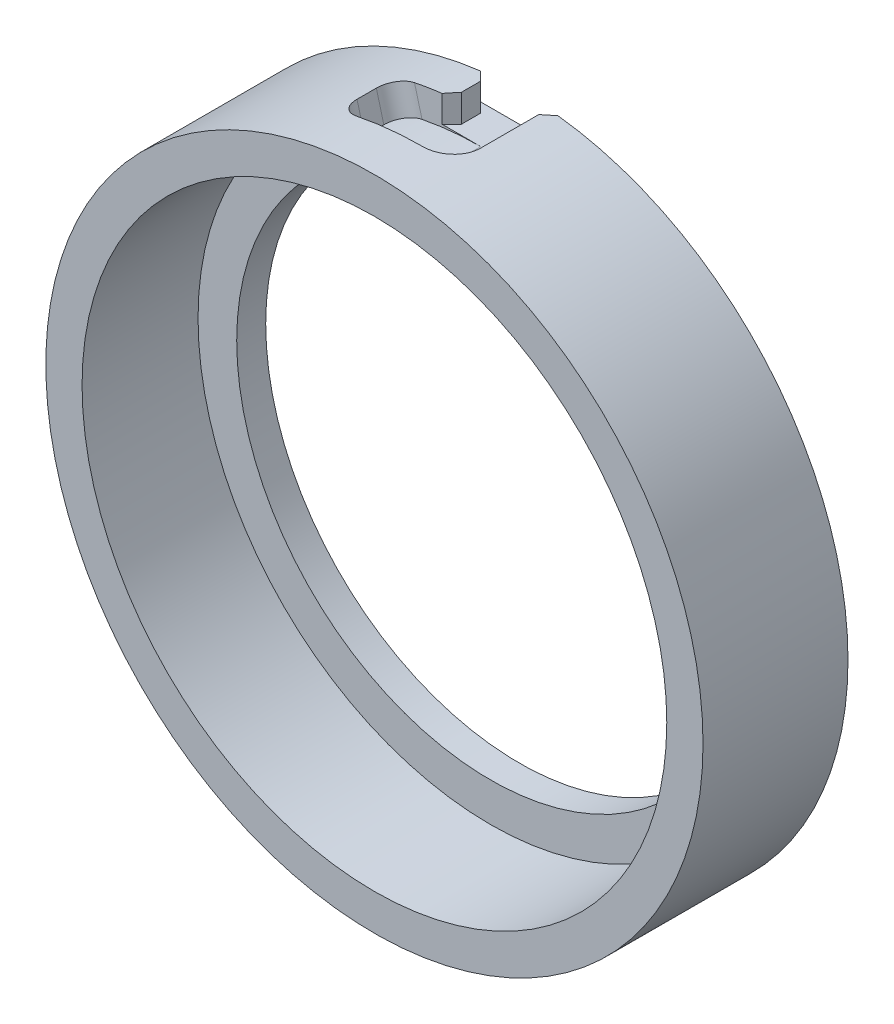
SolidWorks part; units mm, degrees
ref_plane "Спереди" through (0, 0, 0) normal (0, 0, 1) x (1, 0, 0)
ref_plane "Сверху" through (0, 0, 0) normal (0, 1, 0) x (1, 0, 0)
ref_plane "Справа" through (0, 0, 0) normal (1, 0, 0) x (0, 0, -1)
sketch "Эскиз2" plane through (0, 0, 0) normal (1, 0, 0) x (0, 0, -1)
  line L0 (0, 30.25) -> (0, 0) construction
  line L1 (0, 0) -> (15, 0) construction
  line L2 (0, 30.25) -> (12, 30.25)
  line L3 (12, 30.25) -> (12, 26.25)
  line L4 (12, 26.25) -> (15, 26.25)
  line L5 (15, 26.25) -> (15, 34)
  line L6 (15, 34) -> (0, 34)
  line L7 (0, 34) -> (0, 30.25)
  line L8 (15, 0) -> (15, 26.25) construction
  dimension "D1" = 60.5
  dimension "D2" = 68
  dimension "D3" = 15
  dimension "D4" = 4
  dimension "D5" = 3
revolve "Повернуть1" add sketch "Эскиз2" angle 360 about L1
ref_plane "Плоскость1" through (0, 34, 0) normal (0, 1, 0) x (1, 0, 0)
ref_plane "Плоскость2" through (0, -34, 0) normal (0, -1, 0) x (-1, 0, 0)
sketch "Эскиз4" plane through (0, 34, 0) normal (0, 1, 0) x (1, 0, 0)
  line L0 (0, 15) -> (0, 8) construction
  line L1 (34, 15) -> (-34, 15) construction
  line L2 (3, 15) -> (3, 8)
  line L3 (-3, 15) -> (-3, 8)
  arc A0 (3, 15) -> (-3, 15) centre (0, 15) ccw
  arc A1 (-3, 8) -> (3, 8) centre (0, 8) ccw
  point P5 (0, 11.5)
  dimension "D1" = 3
  dimension "D2" = 7
extrude "Вырез-Вытянуть1" cut sketch "Эскиз4" against normal blind 3
sketch "Эскиз5" plane through (0, -34, 0) normal (0, -1, 0) x (-1, 0, 0)
  line L0 (0, 15) -> (0, 8) construction
  line L1 (34, 15) -> (-34, 15) construction
  line L2 (3, 15) -> (3, 8)
  line L3 (-3, 15) -> (-3, 8)
  arc A0 (3, 15) -> (-3, 15) centre (0, 15) ccw
  arc A1 (-3, 8) -> (3, 8) centre (0, 8) ccw
  point P5 (0, 11.5)
  dimension "D1" = 3
  dimension "D2" = 7
extrude "Вырез-Вытянуть2" cut sketch "Эскиз5" against normal blind 3
sketch "Эскиз8" plane through (0, 0, 0) normal (1, 0, 0) x (0, 0, -1)
  line L0 (0, 0) -> (15, 0) construction
  line L2 (5, 34) -> (5, 31)
  line L3 (5, 31) -> (11, 31)
  line L4 (11, 34) -> (11, 31)
  line L5 (0, 30.25) -> (0, -30.25) construction
  line L6 (15, -26.25) -> (15, 26.25) construction
  line L7 (15, -33.8674) -> (15, 33.8674) construction
  line L8 (5, 34) -> (5, 37)
  line L9 (5, 37) -> (11, 37)
  line L10 (11, 37) -> (11, 34)
  spline S0 degree 2 poles (8, 33.8674) (6.5029, 33.8674) (5, 34) knots 0.477898 0.477898 0.477898 1 1 1 weights 0.033867 0.035434 0.037 construction
  dimension "D1" = 3
  dimension "D2" = 6
  dimension "D3" = 4
  dimension "D4" = 3
revolve "Вырез-Повернуть1" cut sketch "Эскиз8" angle 15 about L0
sketch "Эскиз9" plane through (0, 0, 0) normal (1, 0, 0) x (0, 0, -1)
  line L0 (8, -31) -> (15, -31) construction
  line L2 (5, -34) -> (5, -31)
  line L3 (5, -31) -> (11, -31)
  line L4 (11, -34) -> (11, -31)
  line L5 (0, 0) -> (15, 0) construction
  line L6 (0, 30.25) -> (0, -30.25) construction
  line L7 (15, -26.25) -> (15, 26.25) construction
  line L9 (5, -34) -> (5, -37.8305)
  line L10 (5, -37.8305) -> (11, -37.8305)
  line L11 (11, -37.8305) -> (11, -34)
  spline S0 degree 2 poles (5, -34) (6.5029, -33.8674) (8, -33.8674) knots 0 0 0 0.477898 0.477898 0.477898 weights 0.031 0.032434 0.033867 construction
  dimension "D1" = 6
  dimension "D2" = 3
revolve "Вырез-Повернуть2" cut sketch "Эскиз9" angle 15 about L5
chamfer "Фаска1" distance 1 angle 45 4 edges at (-3, -32.4337, -15) (3, -32.4337, -15) (-3, 32.4337, -15) (3, 32.4337, -15)
chamfer "Фаска2" distance 1 angle 45 2 edges at (3, -32.4337, -11) (-3, 32.4337, -11)
fillet "Скругление1" radius 2 2 edges at (8.4116, -31.3926, -5) (8.4116, -31.3926, -11)
fillet "Скругление2" radius 2 2 edges at (-8.4116, 31.3926, -5) (-8.4116, 31.3926, -11)
